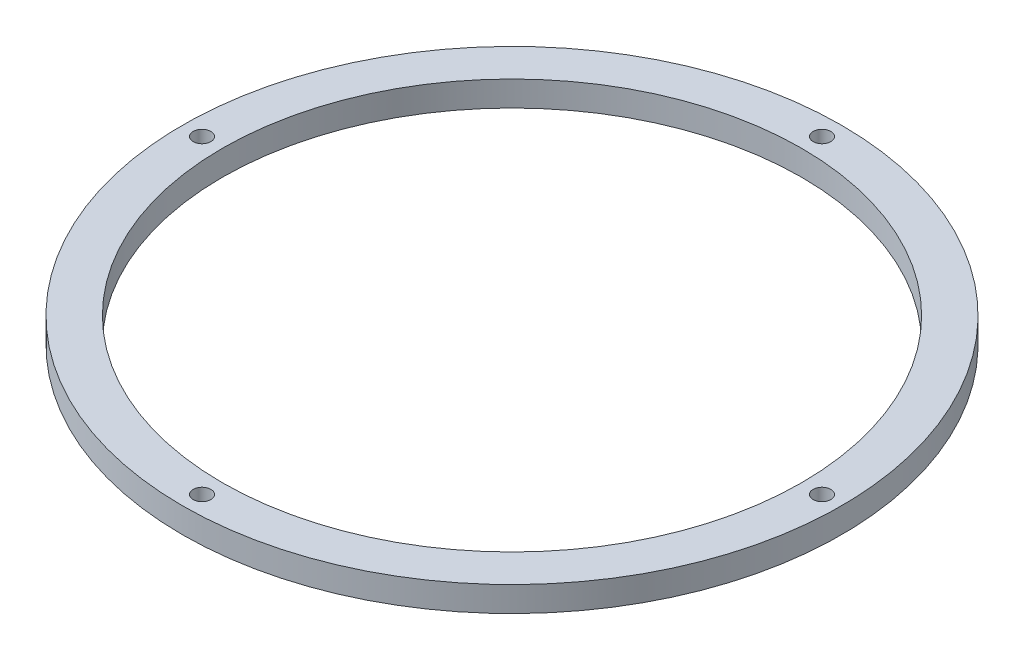
SolidWorks part; units mm, degrees
ref_plane "Front Plane" through (0, 0, 0) normal (0, 0, 1) x (1, 0, 0)
ref_plane "Top Plane" through (0, 0, 0) normal (0, 1, 0) x (1, 0, 0)
ref_plane "Right Plane" through (0, 0, 0) normal (1, 0, 0) x (0, 0, -1)
sketch "Sketch1" plane through (0, 0, 0) normal (0, 1, 0) x (1, 0, 0)
  circle A0 centre (0, 0) radius 111.5
  circle A1 centre (0, 0) radius 98
  dimension "D1" = 223
  dimension "D2" = 196
extrude "Boss-Extrude1" add sketch "Sketch1" along normal blind 8.5
sketch "Sketch2" plane through (0, 8.5, 0) normal (0, 1, 0) x (1, 0, 0)
  circle A0 centre (0, 0) radius 104.875 construction
  circle A1 centre (0, 104.875) radius 3
  circle A2 centre (-104.875, 0) radius 3
  circle A3 centre (104.875, 0) radius 3
  circle A4 centre (0, -104.875) radius 3
  dimension "D1" = 209.75
  dimension "D2" = 6
  dimension "D3" = 6
  dimension "D4" = 6
  dimension "D5" = 6
extrude "Cut-Extrude1" cut sketch "Sketch2" against normal through all contours A1 | A3 | A4 | A2
